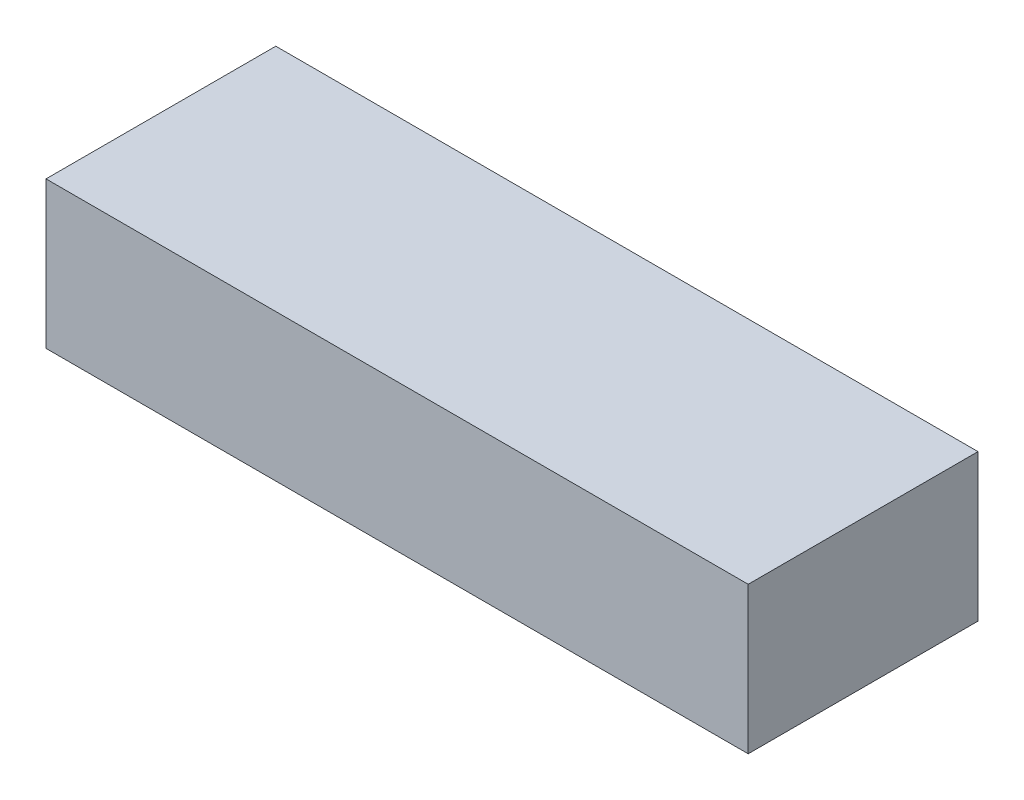
SolidWorks part; units mm, degrees
ref_plane "Front Plane" through (0, 0, 0) normal (0, 0, 1) x (1, 0, 0)
ref_plane "Top Plane" through (0, 0, 0) normal (0, 1, 0) x (1, 0, 0)
ref_plane "Right Plane" through (0, 0, 0) normal (1, 0, 0) x (0, 0, -1)
sketch "Sketch1" plane through (0, 0, 0) normal (0, 1, 0) x (1, 0, 0)
  line L1 (-55, 18) -> (55, 18)
  line L2 (-55, 18) -> (-55, -18)
  line L3 (-55, -18) -> (55, -18)
  line L4 (55, 18) -> (55, -18)
  line L5 (-55, 18) -> (55, -18) construction
  line L6 (-55, -18) -> (55, 18) construction
  point P0 (0, 0)
  dimension "D1" = 36
  dimension "D2" = 110
extrude "Boss-Extrude1" add sketch "Sketch1" along normal blind 23
